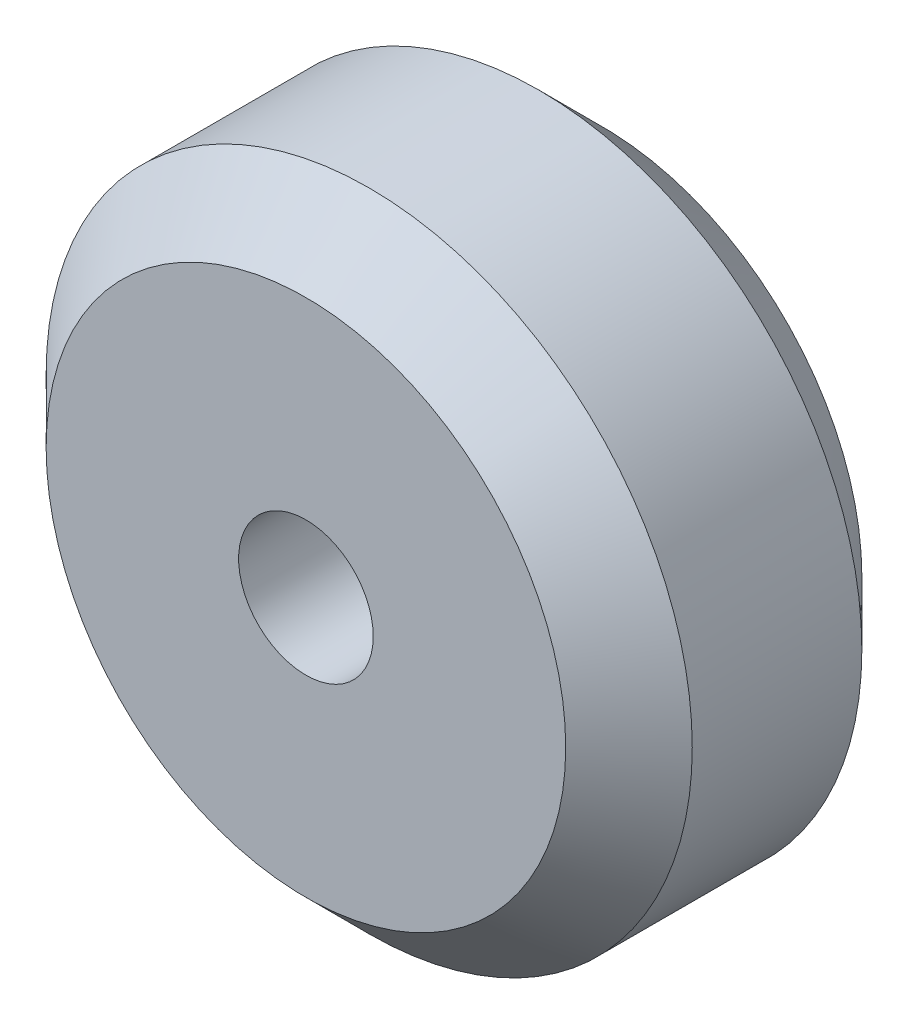
SolidWorks part; units mm, degrees
ref_plane "Front Plane" through (0, 0, 0) normal (0, 0, 1) x (1, 0, 0)
ref_plane "Top Plane" through (0, 0, 0) normal (0, 1, 0) x (1, 0, 0)
ref_plane "Right Plane" through (0, 0, 0) normal (1, 0, 0) x (0, 0, -1)
sketch "Sketch1" plane through (0, 0, 0) normal (0, 1, 0) x (1, 0, 0)
  line L0 (2.5, 0) -> (9.65, 0)
  line L1 (9.65, 0) -> (12, 2.35)
  line L2 (12, 2.35) -> (12, 8.65)
  line L3 (12, 8.65) -> (9.65, 11)
  line L4 (9.65, 11) -> (2.5, 11)
  line L5 (2.5, 11) -> (2.5, 0)
  line L6 (0, 0) -> (0, 13.77) construction
  line L7 (12, 5.5) -> (2.5, 5.5) construction
  point P11 (9.6496, 0)
  point P12 (8.8808, 11)
  point P13 (0, 0)
  dimension "D1" = 6.3
  dimension "D2" = 11
  dimension "D3" = 12
  dimension "D4" = 2.5
  dimension "D5" = 135
revolve "Revolve1" add sketch "Sketch1" angle 360 about L6
